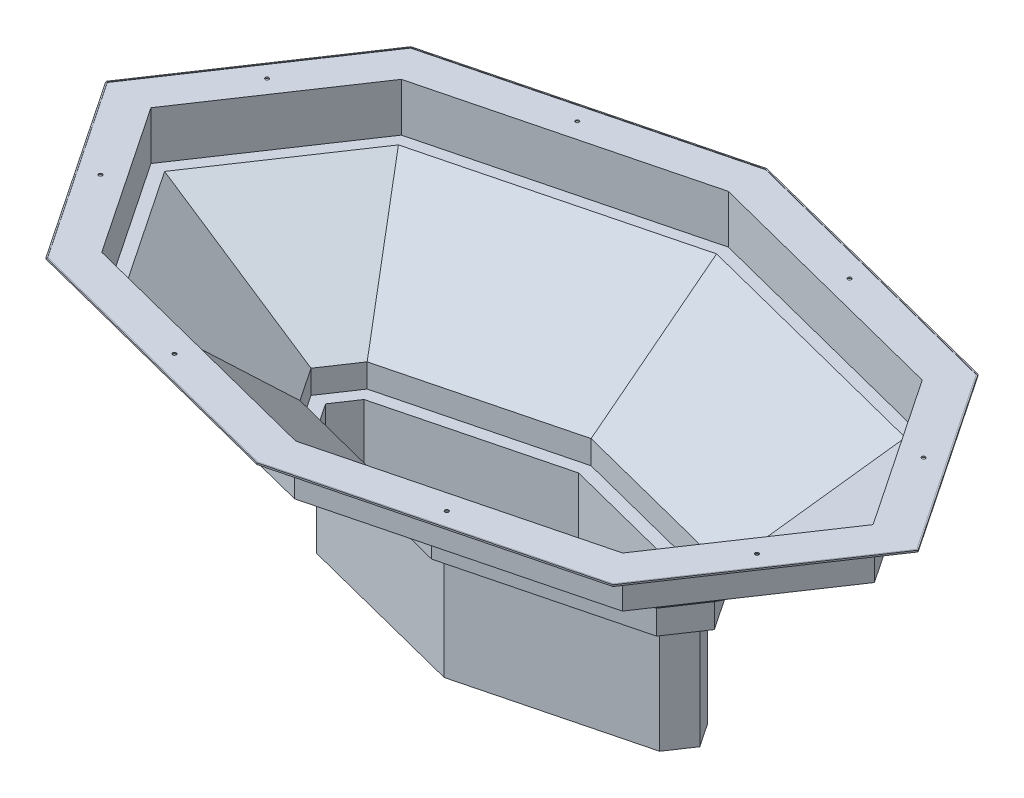
SolidWorks part; units mm, degrees
material "AISI 1020"
ref_plane "Front Plane" through (0, 0, 0) normal (0, 0, 1) x (1, 0, 0)
ref_plane "Top Plane" through (0, 0, 0) normal (0, 1, 0) x (1, 0, 0)
ref_plane "Right Plane" through (0, 0, 0) normal (1, 0, 0) x (0, 0, -1)
sketch "Sketch1" plane through (0, 0, 0) normal (0, 1, 0) x (1, 0, 0)
  line L0 (0, 0) -> (0, 457.2) construction
  line L1 (-762, 0) -> (-549.0794, 317.0112)
  line L2 (-762, 0) -> (0, 0) construction
  line L3 (549.0794, -317.0112) -> (-549.0794, -317.0112) construction
  line L4 (549.0794, -317.0112) -> (549.0794, 317.0112) construction
  line L5 (549.0794, 317.0112) -> (-549.0794, 317.0112) construction
  line L6 (-549.0794, -317.0112) -> (-549.0794, 317.0112) construction
  line L7 (549.0794, -317.0112) -> (-549.0794, 317.0112) construction
  line L8 (549.0794, 317.0112) -> (-549.0794, -317.0112) construction
  line L9 (-549.0794, 317.0112) -> (0, 457.2)
  line L10 (0, 457.2) -> (549.0794, 317.0112)
  line L11 (549.0794, 317.0112) -> (762, 0)
  line L12 (762, 0) -> (549.0794, -317.0112)
  line L13 (549.0794, -317.0112) -> (0, -457.2)
  line L14 (0, -457.2) -> (-549.0794, -317.0112)
  line L15 (-762, 0) -> (-549.0794, -317.0112)
  ellipse E0 centre (0, 0) end of major axis (-762, 0) minor radius 457.2 construction
  dimension "D1" = 762
  dimension "D2" = 457.2
  dimension "D3" = 30
extrude "Boss-Extrude1" add sketch "Sketch1" against normal blind 101.6
sketch "Sketch3" plane through (0, -101.6, 0) normal (0, -1, 0) x (1, 0, 0)
  line L0 (-533.4006, -294.7994) -> (0, -430.9852)
  line L1 (0, -430.9852) -> (533.4006, -294.7994)
  line L2 (533.4006, -294.7994) -> (731.4026, 0)
  line L3 (731.4026, 0) -> (533.4006, 294.7994)
  line L4 (533.4006, 294.7994) -> (0, 430.9852)
  line L5 (0, 430.9852) -> (-533.4006, 294.7994)
  line L6 (-533.4006, 294.7994) -> (-731.4026, 0)
  line L7 (-731.4026, 0) -> (-533.4006, -294.7994)
  line L8 (-549.0794, -317.0112) -> (0, -457.2)
  line L9 (0, -457.2) -> (549.0794, -317.0112)
  line L10 (549.0794, -317.0112) -> (762, 0)
  line L11 (762, 0) -> (549.0794, 317.0112)
  line L12 (549.0794, 317.0112) -> (0, 457.2)
  line L13 (0, 457.2) -> (-549.0794, 317.0112)
  line L14 (-549.0794, 317.0112) -> (-762, 0)
  line L15 (-762, 0) -> (-549.0794, -317.0112)
  line L16 (-549.0794, -317.0112) -> (0, -457.2) construction
  line L17 (0, -457.2) -> (549.0794, -317.0112) construction
  line L18 (549.0794, -317.0112) -> (762, 0) construction
  line L19 (762, 0) -> (549.0794, 317.0112) construction
  line L20 (549.0794, 317.0112) -> (0, 457.2) construction
  line L21 (0, 457.2) -> (-549.0794, 317.0112) construction
  line L22 (-549.0794, 317.0112) -> (-762, 0) construction
  line L23 (-762, 0) -> (-549.0794, -317.0112) construction
  dimension "D1" = 0
  dimension "D2" = 25.4
ref_plane "Plane1" through (0, -304.8, 0) normal (0, -1, 0) x (-1, 0, 0)
sketch "Sketch2" plane through (0, -304.8, 0) normal (0, -1, 0) x (-1, 0, 0)
  line L0 (-762, 0) -> (-549.0794, -317.0112) construction
  line L1 (-425.4287, 0) -> (-376.6117, -72.6822)
  line L2 (-376.6117, -72.6822) -> (0, -168.8372)
  line L3 (0, -168.8372) -> (376.6117, -72.6822)
  line L4 (376.6117, -72.6822) -> (425.4287, 0)
  line L5 (425.4287, 0) -> (376.6117, 72.6822)
  line L6 (376.6117, 72.6822) -> (0, 168.8372)
  line L7 (0, 168.8372) -> (-376.6117, 72.6822)
  line L8 (549.0794, 317.0112) -> (0, 457.2)
  line L9 (762, 0) -> (549.0794, 317.0112)
  line L10 (549.0794, -317.0112) -> (762, 0)
  line L11 (0, -457.2) -> (549.0794, -317.0112)
  line L12 (-549.0794, -317.0112) -> (0, -457.2)
  line L13 (-762, 0) -> (-549.0794, -317.0112)
  line L14 (-549.0794, 317.0112) -> (-762, 0)
  line L15 (0, 457.2) -> (-549.0794, 317.0112)
  line L16 (549.0794, 317.0112) -> (0, 457.2) construction
  line L17 (762, 0) -> (549.0794, 317.0112) construction
  line L18 (549.0794, -317.0112) -> (762, 0) construction
  line L19 (0, -457.2) -> (549.0794, -317.0112) construction
  line L20 (-549.0794, -317.0112) -> (0, -457.2) construction
  line L21 (-376.6117, 72.6822) -> (-425.4287, 0)
  line L22 (-549.0794, 317.0112) -> (-762, 0) construction
  line L23 (0, 457.2) -> (-549.0794, 317.0112) construction
  dimension "D2" = 279.4
  dimension "D1" = 0
loft "Loft1" add profiles "Sketch3", "Sketch2"
sketch "Sketch4" plane through (0, -304.8, 0) normal (0, -1, 0) x (1, 0, 0)
  line L8 (0, -168.8372) -> (376.6117, -72.6822)
  line L9 (0, -168.8372) -> (376.6117, -72.6822)
  line L10 (376.6117, -72.6822) -> (425.4287, 0)
  line L11 (376.6117, -72.6822) -> (425.4287, 0)
  line L12 (425.4287, 0) -> (376.6117, 72.6822)
  line L13 (425.4287, 0) -> (376.6117, 72.6822)
  line L14 (376.6117, 72.6822) -> (0, 168.8372)
  line L15 (376.6117, 72.6822) -> (0, 168.8372)
  line L16 (0, 168.8372) -> (-376.6117, 72.6822)
  line L17 (0, 168.8372) -> (-376.6117, 72.6822)
  line L18 (-376.6117, 72.6822) -> (-425.4287, 0)
  line L19 (-376.6117, 72.6822) -> (-425.4287, 0)
  line L20 (-425.4287, 0) -> (-376.6117, -72.6822)
  line L21 (-425.4287, 0) -> (-376.6117, -72.6822)
  line L22 (-376.6117, -72.6822) -> (0, -168.8372)
  line L23 (-376.6117, -72.6822) -> (0, -168.8372)
  dimension "D1" = 0
extrude "Boss-Extrude2" add sketch "Sketch4" along normal blind 50.8
sketch "Sketch5" plane through (0, 0, 0) normal (0, 1, 0) x (1, 0, 0)
  line L0 (0, 535.8444) -> (-596.1161, 383.6463)
  line L1 (-596.1161, 383.6463) -> (-853.7922, 0)
  line L2 (-853.7922, 0) -> (-596.1161, -383.6463)
  line L3 (-596.1161, -383.6463) -> (0, -535.8444)
  line L4 (0, -535.8444) -> (596.1161, -383.6463)
  line L5 (596.1161, -383.6463) -> (853.7922, 0)
  line L6 (853.7922, 0) -> (596.1161, 383.6463)
  line L7 (596.1161, 383.6463) -> (0, 535.8444)
  line L8 (0, 457.2) -> (-549.0794, 317.0112)
  line L9 (-549.0794, 317.0112) -> (-762, 0)
  line L10 (-762, 0) -> (-549.0794, -317.0112)
  line L11 (-549.0794, -317.0112) -> (0, -457.2)
  line L12 (0, -457.2) -> (549.0794, -317.0112)
  line L13 (549.0794, -317.0112) -> (762, 0)
  line L14 (762, 0) -> (549.0794, 317.0112)
  line L15 (549.0794, 317.0112) -> (0, 457.2)
  line L16 (0, 457.2) -> (-549.0794, 317.0112) construction
  line L17 (-549.0794, 317.0112) -> (-762, 0) construction
  line L18 (-762, 0) -> (-549.0794, -317.0112) construction
  line L19 (-549.0794, -317.0112) -> (0, -457.2) construction
  line L20 (0, -457.2) -> (549.0794, -317.0112) construction
  line L21 (549.0794, -317.0112) -> (762, 0) construction
  line L22 (762, 0) -> (549.0794, 317.0112) construction
  line L23 (549.0794, 317.0112) -> (0, 457.2) construction
  dimension "D1" = 0
  dimension "D2" = 76.2
extrude "Boss-Extrude3" add sketch "Sketch5" along normal blind 3.175
sketch "Sketch6" plane through (0, -355.6, 0) normal (0, -1, 0) x (1, 0, 0)
  line L0 (0, 142.6224) -> (-360.9328, 50.4705)
  line L1 (-360.9328, 50.4705) -> (-394.8313, 0)
  line L2 (-394.8313, 0) -> (-360.9328, -50.4705)
  line L3 (-360.9328, -50.4705) -> (0, -142.6224)
  line L4 (0, -142.6224) -> (360.9328, -50.4705)
  line L5 (360.9328, -50.4705) -> (394.8313, 0)
  line L6 (394.8313, 0) -> (360.9328, 50.4705)
  line L7 (360.9328, 50.4705) -> (0, 142.6224)
  line L8 (376.6117, -72.6822) -> (425.4287, 0)
  line L9 (425.4287, 0) -> (376.6117, 72.6822)
  line L10 (376.6117, 72.6822) -> (0, 168.8372)
  line L11 (0, 168.8372) -> (-376.6117, 72.6822)
  line L12 (-376.6117, 72.6822) -> (-425.4287, 0)
  line L13 (-425.4287, 0) -> (-376.6117, -72.6822)
  line L14 (-376.6117, -72.6822) -> (0, -168.8372)
  line L15 (0, -168.8372) -> (376.6117, -72.6822)
  line L16 (376.6117, -72.6822) -> (425.4287, 0) construction
  line L17 (425.4287, 0) -> (376.6117, 72.6822) construction
  line L18 (376.6117, 72.6822) -> (0, 168.8372) construction
  line L19 (0, 168.8372) -> (-376.6117, 72.6822) construction
  line L20 (-376.6117, 72.6822) -> (-425.4287, 0) construction
  line L21 (-425.4287, 0) -> (-376.6117, -72.6822) construction
  line L22 (-376.6117, -72.6822) -> (0, -168.8372) construction
  line L23 (0, -168.8372) -> (376.6117, -72.6822) construction
  dimension "D1" = 0
  dimension "D2" = 25.4
extrude "Boss-Extrude4" add sketch "Sketch6" along normal blind 228.6
shell "Shell2" thickness 2.3813
sketch "Sketch7" [suppressed] plane through (0, 0, 0) normal (0, 1, 0) x (1, 0, 0)
  line L0 (-357.6619, 144.0827) -> (0, 276.108) construction
  line L1 (-423.0411, 0) -> (-357.6619, 144.0827) construction
  line L2 (-357.6619, -144.0827) -> (-423.0411, 0) construction
  line L3 (-357.6619, -144.0827) -> (0, -276.108) construction
  line L4 (0, -276.108) -> (357.6619, -144.0827) construction
  line L5 (357.6619, -144.0827) -> (423.0411, 0) construction
  line L6 (357.6619, 144.0827) -> (423.0411, 0) construction
  line L7 (357.6619, 144.0827) -> (0, 276.108) construction
  line L8 (-357.6619, 144.0827) -> (0, 276.108) construction
  line L9 (-423.0411, 0) -> (-357.6619, 144.0827) construction
  line L10 (-357.6619, -144.0827) -> (-423.0411, 0) construction
  line L11 (-357.6619, -144.0827) -> (0, -276.108) construction
  line L12 (0, -276.108) -> (357.6619, -144.0827) construction
  line L13 (357.6619, -144.0827) -> (423.0411, 0) construction
  line L14 (357.6619, 144.0827) -> (423.0411, 0) construction
  line L15 (357.6619, 144.0827) -> (0, 276.108) construction
sketch "Sketch8" plane through (0, 3.175, 0) normal (0, 1, 0) x (1, 0, 0)
  line L0 (572.5978, 350.3287) -> (0, 496.5222) construction
  line L1 (0, 496.5222) -> (-572.5978, 350.3287) construction
  line L2 (-572.5978, 350.3287) -> (-807.8961, 0) construction
  line L3 (-807.8961, 0) -> (-572.5978, -350.3287) construction
  line L4 (-572.5978, -350.3287) -> (0, -496.5222) construction
  line L5 (0, -496.5222) -> (572.5978, -350.3287) construction
  line L6 (572.5978, -350.3287) -> (807.8961, 0) construction
  line L7 (807.8961, 0) -> (572.5978, 350.3287) construction
  line L8 (596.1161, 383.6463) -> (0, 535.8444)
  line L9 (0, 535.8444) -> (-596.1161, 383.6463)
  line L10 (-596.1161, 383.6463) -> (-853.7922, 0)
  line L11 (-853.7922, 0) -> (-596.1161, -383.6463)
  line L12 (-596.1161, -383.6463) -> (0, -535.8444)
  line L13 (0, -535.8444) -> (596.1161, -383.6463)
  line L14 (596.1161, -383.6463) -> (853.7922, 0)
  line L15 (853.7922, 0) -> (596.1161, 383.6463)
  line L16 (596.1161, 383.6463) -> (0, 535.8444) construction
  line L17 (0, 535.8444) -> (-596.1161, 383.6463) construction
  line L18 (-596.1161, 383.6463) -> (-853.7922, 0) construction
  line L19 (-853.7922, 0) -> (-596.1161, -383.6463) construction
  line L20 (-596.1161, -383.6463) -> (0, -535.8444) construction
  line L21 (0, -535.8444) -> (596.1161, -383.6463) construction
  line L22 (596.1161, -383.6463) -> (853.7922, 0) construction
  line L23 (853.7922, 0) -> (596.1161, 383.6463) construction
  circle A0 centre (-286.2989, 423.4255) radius 3.81
  circle A1 centre (286.2989, 423.4255) radius 3.81
  circle A2 centre (690.2469, 175.1644) radius 3.81
  circle A3 centre (690.2469, -175.1644) radius 3.81
  circle A4 centre (286.2989, -423.4255) radius 3.81
  circle A5 centre (-286.2989, -423.4255) radius 3.81
  circle A6 centre (-690.2469, -175.1644) radius 3.81
  circle A7 centre (-690.2469, 175.1644) radius 3.81
  dimension "D3" = 7.62
  dimension "D1" = 0
  dimension "D2" = 38.1
extrude "Cut-Extrude1" cut sketch "Sketch8" against normal up to next
sketch "Sketch9" plane through (0, -584.2, 0) normal (0, -1, 0) x (1, 0, 0)
  line L1 (1009.9465, -645.8443) -> (-874.8808, -645.8443)
  line L2 (1009.9465, -645.8443) -> (1009.9465, 608.3567)
  line L3 (1009.9465, 608.3567) -> (-874.8808, 608.3567)
  line L4 (-874.8808, -645.8443) -> (-874.8808, 608.3567)
extrude "Boss-Extrude5" [suppressed] add sketch "Sketch9" against normal blind 579.12 separate body
combine bodies "Combine1" [suppressed] operation type subtract main body 107 bodies to subtract 106
